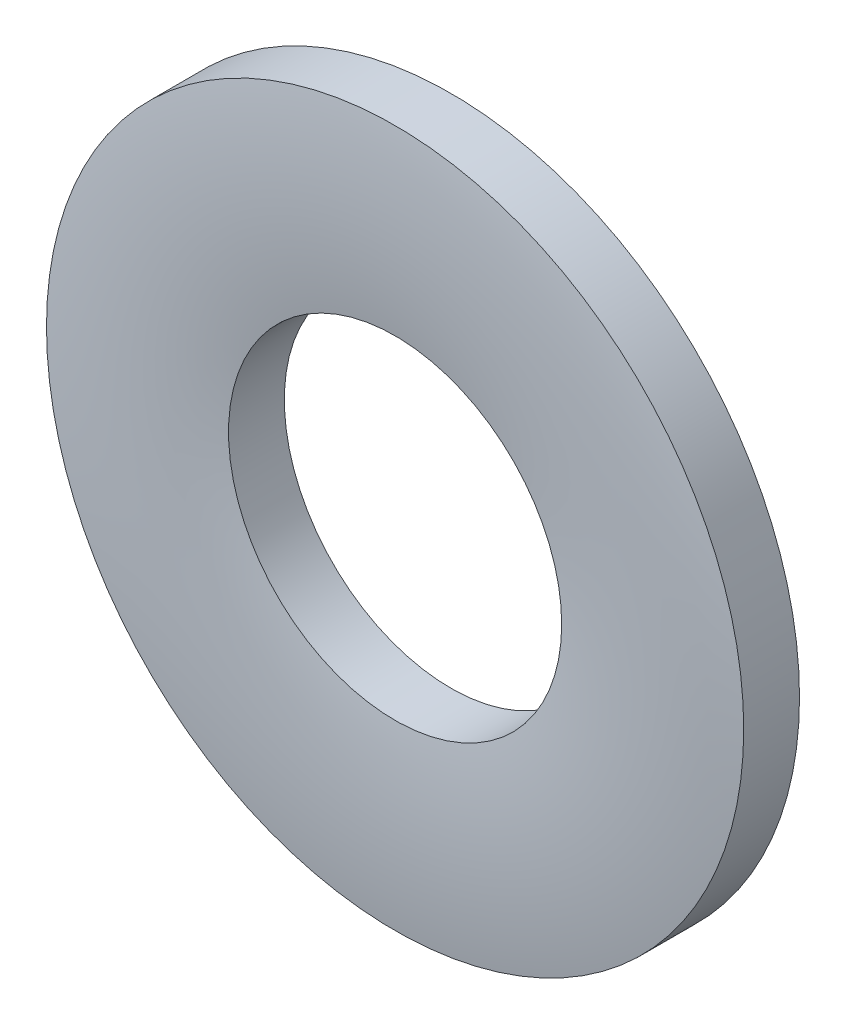
SolidWorks part; units mm, degrees
ref_plane "Front Plane" through (0, 0, 0) normal (0, 0, 1) x (1, 0, 0)
ref_plane "Top Plane" through (0, 0, 0) normal (0, 1, 0) x (1, 0, 0)
ref_plane "Right Plane" through (0, 0, 0) normal (1, 0, 0) x (0, 0, -1)
sketch "Sketch1" plane through (0, 0, 0) normal (0, 0, 1) x (1, 0, 0)
  circle A0 centre (0, 0) radius 2.15
  circle A1 centre (0, 0) radius 4.5
  dimension "ID" = 4.3
  dimension "OD" = 9
sketch "Sketch2" plane through (0, 0, 0) normal (1, 0, 0) x (0, 0, -1)
  line L0 (-0.4, 4.5) -> (0.4, 4.5) construction
  line L1 (-0.4, 0) -> (0.4, 0) construction
  point P2 (0, 4.5)
  dimension "Thickness Range" = 0.8
sketch "Sketch3" plane through (0, 0, 0) normal (1, 0, 0) x (0, 0, -1)
  line L0 (0.4, 4.5) -> (-0.32, 4.5)
  line L1 (0.4, 2.15) -> (-0.32, 2.15)
  line L2 (0.4, 2.15) -> (0.4, 4.5)
  line L3 (-0.4, 4.5) -> (-0.4, 2.15) construction
  arc A0 (-0.32, 2.15) -> (-0.32, 4.5) centre (8.2689, 3.325) cw
  point P9 (0, 2.15)
  dimension "D1" = 0.08
revolve "Revolve1" add sketch "Sketch3" angle 360 about L1
equation "\"D1@Sketch3\"=\"Thickness Range@Sketch2\"*.1"
